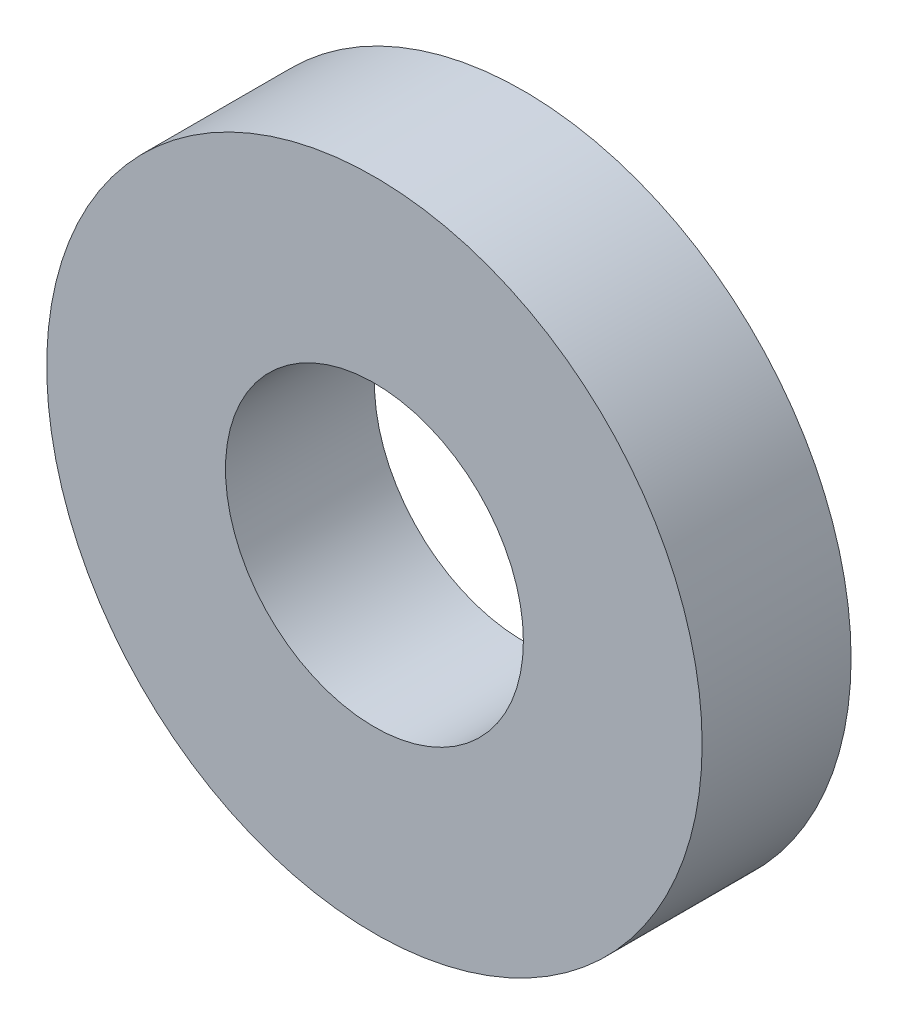
SolidWorks part; units mm, degrees
ref_plane "Front Plane" through (0, 0, 0) normal (0, 0, 1) x (1, 0, 0)
ref_plane "Top Plane" through (0, 0, 0) normal (0, 1, 0) x (1, 0, 0)
ref_plane "Right Plane" through (0, 0, 0) normal (1, 0, 0) x (0, 0, -1)
sketch "Sketch1" plane through (0, 0, 0) normal (0, 0, 1) x (1, 0, 0)
  circle A0 centre (0, 0) radius 6
  circle A1 centre (0, 0) radius 13.2
extrude "Boss-Extrude1" add sketch "Sketch1" along normal blind 6
sketch "Sketch2" plane through (0, 0, 6) normal (0, 0, 1) x (1, 0, 0)
  line L0 (0, 0) -> (0, 15.2) construction
  line L1 (-1.8199, 15.2) -> (0, 0) construction
  line L2 (1.8199, 15.2) -> (0, 0) construction
  arc A0 (-1.8199, 12) -> (1.8199, 12) centre (0, 0) cw
  arc A1 (-6.8199, 11.3018) -> (6.8199, 11.3018) centre (0, 0) cw
  arc A2 (-1.8199, 10.512) -> (1.8199, 10.512) centre (0, 0) cw
  arc A3 (-6.8199, 11.3018) -> (-1.8199, 12) centre (-4.3199, 11.6509) ccw
  arc A4 (6.8199, 11.3018) -> (1.8199, 10.512) centre (4.3199, 10.9069) ccw
sketch "Sketch3" plane through (0, 0, 0) normal (0, 0, 1) x (1, 0, 0)
  circle A0 centre (0, 0) radius 6
  circle A1 centre (0, 0) radius 13.2
